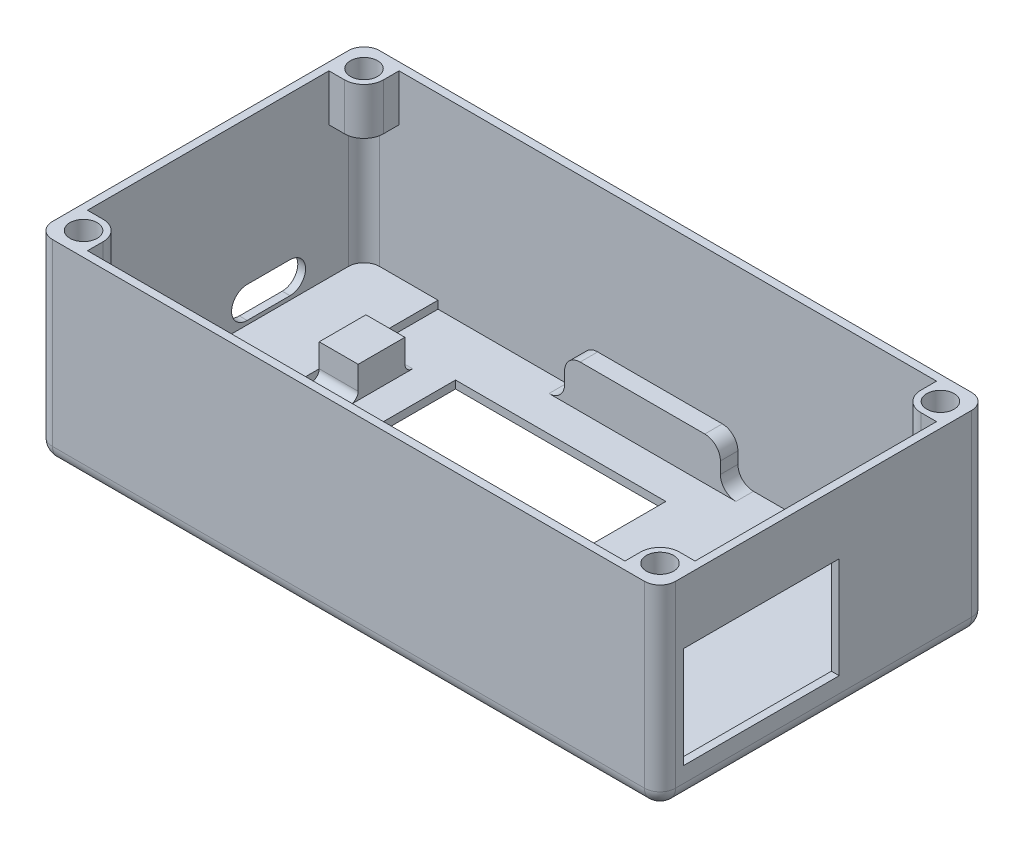
SolidWorks part; units mm, degrees
ref_plane "Front Plane" through (0, 0, 0) normal (0, 0, 1) x (1, 0, 0)
ref_plane "Top Plane" through (0, 0, 0) normal (0, 1, 0) x (1, 0, 0)
ref_plane "Right Plane" through (0, 0, 0) normal (1, 0, 0) x (0, 0, -1)
sketch "Sketch1" plane through (0, 0, 0) normal (0, 1, 0) x (1, 0, 0)
  line L1 (-40, -21) -> (40, -21)
  line L2 (-40, -21) -> (-40, 21)
  line L3 (-40, 21) -> (40, 21)
  line L4 (40, -21) -> (40, 21)
  line L5 (-40, -21) -> (40, 21) construction
  line L6 (-40, 21) -> (40, -21) construction
  point P0 (0, 0)
  dimension "D1" = 80
  dimension "D2" = 42
extrude "Boss-Extrude1" add sketch "Sketch1" along normal blind 25
sketch "Sketch6" plane through (0, 25, 0) normal (0, 1, 0) x (1, 0, 0)
  line L0 (40, -21) -> (40, 21) construction
  line L1 (-39, 20) -> (39, 20)
  line L2 (-39, 20) -> (-39, -20)
  line L3 (-39, -20) -> (39, -20)
  line L4 (39, 20) -> (39, -20)
  line L5 (-39, 20) -> (39, -20) construction
  line L6 (-39, -20) -> (39, 20) construction
  line L7 (-40, -21) -> (40, -21) construction
  point P0 (0, 0)
  dimension "D1" = 1
  dimension "D2" = 1
extrude "Cut-Extrude6" cut sketch "Sketch6" against normal offset from surface (24 mm away) 1 up to face at (0, 0, 0)
sketch "Sketch7" plane through (0, 1, 0) normal (0, 1, 0) x (1, 0, 0)
  line L0 (-40, 21) -> (-40, -21) construction
  line L1 (-24.5, 17.75) -> (9, 17.75)
  line L2 (-24.5, 17.75) -> (-24.5, -2.25)
  line L3 (-24.5, -2.25) -> (9, -2.25)
  line L4 (9, 17.75) -> (9, -2.25)
  line L5 (-24.5, 17.75) -> (9, -2.25) construction
  line L6 (-24.5, -2.25) -> (9, 17.75) construction
  line L8 (39, 20) -> (-39, 20) construction
  point P0 (-7.75, 7.75)
  dimension "D1" = 20
  dimension "D2" = 33.5
  dimension "D3" = 15.5
  dimension "D4" = 2.25
extrude "Cut-Extrude7" cut sketch "Sketch7" against normal up to next
sketch "Sketch8" plane through (0, 1, 0) normal (0, 1, 0) x (1, 0, 0)
  line L0 (-24.5, 17.75) -> (-24.5, -2.25) construction
  line L1 (-29.5, 10.75) -> (-24.5, 10.75)
  line L2 (-29.5, 10.75) -> (-29.5, 4.75)
  line L3 (-29.5, 4.75) -> (-24.5, 4.75)
  line L4 (-24.5, 10.75) -> (-24.5, 4.75)
  line L5 (-29.5, 10.75) -> (-24.5, 4.75) construction
  line L6 (-29.5, 4.75) -> (-24.5, 10.75) construction
  point P0 (-27, 7.75)
  point P5 (-29.2666, 5.2771)
  point P6 (0, 0)
  point P9 (-24.5, 7.75)
  dimension "D1" = 6
  dimension "D2" = 5
extrude "Boss-Extrude2" add sketch "Sketch8" along normal blind 4
sketch "Sketch9" plane through (0, 1, 0) normal (0, 1, 0) x (1, 0, 0)
  line L1 (-39, 20) -> (-29.5, 20)
  line L2 (-39, 20) -> (-39, -5.25)
  line L3 (-39, -5.25) -> (-29.5, -5.25)
  line L4 (-29.5, 20) -> (-29.5, -5.25)
  line L5 (-29.5, 10.75) -> (-29.5, 4.75) construction
  line L6 (-24.5, -2.25) -> (9, -2.25) construction
  point P5 (-30.5, -9.7447)
  dimension "D1" = 3
extrude "Boss-Extrude3" add sketch "Sketch9" along normal blind 1
fillet "Fillet1" radius 1 2 edges at (-27, 1, -10.75) (-27, 1, -4.75)
fillet "Fillet3" radius 2 8 edges at (-39, 13, 20) (39, 13, 20) (39, 13, -20) (-39, 13.5, -20) (40, 12.5, -21) (-40, 12.5, -21) (-40, 12.5, 21) (40, 12.5, 21)
sketch "Sketch16" plane through (0, 1, 0) normal (0, 1, 0) x (1, 0, 0)
  line L0 (39, -18) -> (39, 18) construction
  line L1 (24, -2.25) -> (37, -2.25)
  line L2 (24, -2.25) -> (24, 17.75)
  line L3 (24, 17.75) -> (37, 17.75)
  line L4 (37, -2.25) -> (37, 17.75)
  line L5 (24, -2.25) -> (37, 17.75) construction
  line L6 (24, 17.75) -> (37, -2.25) construction
  line L9 (9, 17.75) -> (-24.5, 17.75) construction
  point P0 (30.5, 7.75)
  point P5 (0, 0)
  point P6 (24.5342, -5.7241)
  dimension "D1" = 13
  dimension "D2" = 20
  dimension "D3" = 2
extrude "Cut-Extrude11" [suppressed] cut sketch "Sketch16" against normal up to next
sketch "Sketch12" plane through (-39, 0, 0) normal (1, 0, 0) x (0, 0, -1)
  line L0 (7.75, 1) -> (7.75, 4.5) construction
  line L4 (-5.25, 1) -> (-18, 1) construction
  line L5 (5, 4.5) -> (10.5, 4.5) construction
  line L6 (5, 6.5) -> (10.5, 6.5)
  line L7 (5, 2.5) -> (10.5, 2.5)
  line L10 (10.75, 5) -> (4.75, 5) construction
  line L11 (10.75, 5) -> (4.75, 5) construction
  arc A0 (5, 6.5) -> (5, 2.5) centre (5, 4.5) ccw
  arc A1 (10.5, 2.5) -> (10.5, 6.5) centre (10.5, 4.5) ccw
  point P4 (7.75, 4.5)
  point P11 (3, 4.5)
  point P12 (12.5, 4.5)
  point P15 (0, 0)
  point P16 (7.75, 5)
  point P17 (10.5, 2.5)
  dimension "D1" = 3.5
  dimension "D2" = 4
  dimension "D3" = 9.5
extrude "Cut-Extrude8" cut sketch "Sketch12" against normal up to next
sketch "Sketch18" plane through (0, 1, 0) normal (0, 1, 0) x (1, 0, 0)
  line L0 (37, 20) -> (-29.5, 20) construction
  line L1 (9, 17.75) -> (-11, 17.75)
  line L2 (9, 17.75) -> (9, 20)
  line L3 (9, 20) -> (-11, 20)
  line L4 (-11, 17.75) -> (-11, 20)
  line L5 (-39, -5.25) -> (-29.5, -5.25) construction
  line L6 (9, -2.25) -> (-11, -2.25)
  line L7 (9, -2.25) -> (9, -5.25)
  line L8 (9, -5.25) -> (-11, -5.25)
  line L9 (-11, -2.25) -> (-11, -5.25)
  point P14 (0, 0)
  dimension "D1" = 20
extrude "Boss-Extrude5" add sketch "Sketch18" along normal up to surface (5.5 mm away) up to face at (-39.5, 6.5, -7.75)
fillet "Fillet5" radius 2 8 edges at (-11, 1, 3.75) (9, 1, 3.75) (9, 6.5, 3.75) (-11, 6.5, 3.75) (9, 6.5, -18.875) (-11, 6.5, -18.875) (-11, 1, -18.875) (9, 1, -18.875)
sketch "Sketch19" plane through (-40, 0, 0) normal (-1, 0, 0) x (0, 0, 1)
  line L0 (13, 0) -> (13, 7.5) construction
  line L1 (-19, 0) -> (19, 0) construction
  line L3 (19, 0) -> (19, 25) construction
  line L5 (10, 8.75) -> (10, 6.25)
  arc A0 (10, 6.25) -> (10, 8.75) centre (13, 7.5) ccw
  arc A1 (10, 8.75) -> (10, 6.25) centre (13, 7.5) ccw construction
  point P7 (13, 3.75)
  dimension "D3" = 6.5
  dimension "D1" = 6
  dimension "D2" = 7.5
  dimension "D4" = 3
extrude "Cut-Extrude12" cut sketch "Sketch19" against normal up to next
sketch "Sketch20" plane through (0, 25, 0) normal (0, 1, 0) x (1, 0, 0)
  line L0 (37, 20) -> (-37, 20) construction
  line L4 (-39, 18) -> (-39, -5.25) construction
  line L5 (-34.5, 20) -> (-37, 20)
  line L9 (-39, 18) -> (-39, 15.5)
  line L10 (-37, 15.5) -> (-39, 15.5)
  line L11 (-34.5, 18) -> (-34.5, 20)
  arc A3 (-37, 20) -> (-39, 18) centre (-37, 18) ccw construction
  arc A7 (-37, 20) -> (-39, 18) centre (-37, 18) ccw
  arc A8 (-37, 15.5) -> (-34.5, 18) centre (-37, 18) ccw
  dimension "D1" = 5
extrude "Boss-Extrude6" add sketch "Sketch20" against normal blind 6
sketch "Sketch22" plane through (0, 25, 0) normal (0, 1, 0) x (1, 0, 0)
  line L4 (40, -19) -> (40, 19)
  line L5 (38, 21) -> (-38, 21)
  line L6 (-40, 19) -> (-40, -19)
  line L7 (-38, -21) -> (38, -21)
  line L8 (40, -19) -> (40, 19)
  line L9 (38, 21) -> (-38, 21)
  line L10 (-40, 19) -> (-40, -19)
  line L11 (-38, -21) -> (38, -21)
  circle A0 centre (-37, 18) radius 1.75
  arc A4 (40, 19) -> (38, 21) centre (38, 19) ccw
  arc A5 (-38, 21) -> (-40, 19) centre (-38, 19) ccw
  arc A6 (-40, -19) -> (-38, -21) centre (-38, -19) ccw
  arc A7 (38, -21) -> (40, -19) centre (38, -19) ccw
  arc A8 (40, 19) -> (38, 21) centre (38, 19) ccw
  arc A9 (-38, 21) -> (-40, 19) centre (-38, 19) ccw
  arc A10 (-40, -19) -> (-38, -21) centre (-38, -19) ccw
  arc A11 (38, -21) -> (40, -19) centre (38, -19) ccw
  point P2 (-37, 18)
  dimension "D2" = 3.5
  dimension "D1" = 0
extrude "Cut-Extrude13" cut sketch "Sketch22" against normal up to next contours A0
mirror "Mirror1" about plane through (0, 0, 0) normal (0, 0, 1) of "Cut-Extrude13", "Boss-Extrude6"
mirror "Mirror3" about plane through (0, 0, 0) normal (1, 0, 0) of "Mirror1", "Cut-Extrude13", "Boss-Extrude6"
fillet "Fillet6" radius 2 8 edges at (-39.4142, 0, 20.4142) (-40, 0, 0) (-39.4142, 0, -20.4142) (0, 0, -21) (39.4142, 0, -20.4142) (40, 0, 0) (39.4142, 0, 20.4142) (0, 0, 21)
sketch "Sketch23" plane through (0, 0, 0) normal (0, -1, 0) x (1, 0, 0)
  line L0 (-20.5, 2.25) -> (-20.5, -13.25)
  line L1 (-24.5, 2.25) -> (9, 2.25) construction
  line L2 (-20.5, -13.25) -> (6.5, -13.25)
  line L3 (6.5, -13.25) -> (6.5, 2.25)
  line L4 (6.5, 2.25) -> (9, 2.25)
  line L5 (9, 2.25) -> (9, -17.75)
  line L6 (9, -17.75) -> (-24.5, -17.75)
  line L7 (-24.5, -17.75) -> (-24.5, 2.25)
  line L8 (-24.5, 2.25) -> (-20.5, 2.25)
  point P12 (-23.5854, 3.25)
  dimension "D1" = 4.5
  dimension "D2" = 4
  dimension "D3" = 2.5
extrude "Boss-Extrude7" add sketch "Sketch23" against normal up to surface (1 mm away) up to face at (-22.3333, 1, -16.5)
sketch "Sketch24" plane through (40, 0, 0) normal (1, 0, 0) x (0, 0, -1)
  line L0 (-19, 25) -> (-19, 2) construction
  line L1 (-18, 17) -> (2, 17)
  line L2 (-18, 17) -> (-18, 4)
  line L3 (-18, 4) -> (2, 4)
  line L4 (2, 17) -> (2, 4)
  line L5 (-18, 17) -> (2, 4) construction
  line L6 (-18, 4) -> (2, 17) construction
  line L7 (-19, 2) -> (19, 2) construction
  point P0 (-8, 10.5)
  dimension "D1" = 13
  dimension "D2" = 20
  dimension "D3" = 1
  dimension "D4" = 2
extrude "Cut-Extrude14" cut sketch "Sketch24" against normal up to next
